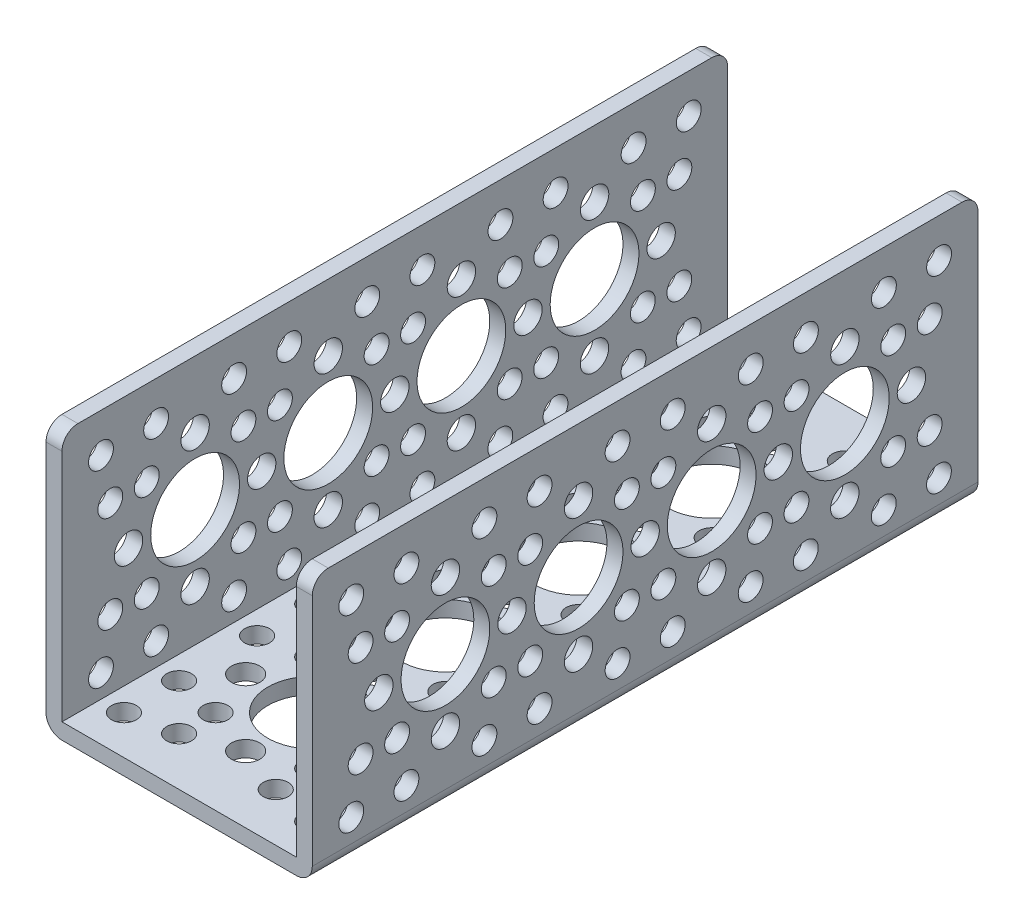
SolidWorks part; units mm, degrees
ref_plane "Front Plane" through (0, 0, 0) normal (0, 0, 1) x (1, 0, 0)
ref_plane "Top Plane" through (0, 0, 0) normal (0, 1, 0) x (1, 0, 0)
ref_plane "Right Plane" through (0, 0, 0) normal (1, 0, 0) x (0, 0, -1)
sketch "Sketch1" plane through (0, 0, 0) normal (0, 0, 1) x (1, 0, 0)
  line L1 (0, 0) -> (38.1, 0)
  line L2 (0, 0) -> (0, 38.1)
  line L4 (38.1, 0) -> (38.1, 38.1)
extrude "Extrude-Thin1" add sketch "Sketch1" along normal blind 95.25 thin thin type one direction wall 2.286
sketch "Sketch3" plane through (0, 0, 0) normal (0, -1, 0) x (1, 0, 0)
  line L0 (19.05, 0) -> (19.05, 95.25) construction
  line L1 (38.1, 0) -> (0, 0) construction
  line L2 (38.1, 95.25) -> (0, 95.25) construction
  circle B0 centre (19.05, 38.1084) radius 6.35
  circle B1 centre (9.525, 38.1084) radius 2.032
  circle B2 centre (28.575, 38.1084) radius 2.032
  circle B3 centre (19.05, 57.1584) radius 6.35
  circle B4 centre (9.525, 57.1584) radius 2.032
  circle B5 centre (28.575, 57.1584) radius 2.032
  circle B6 centre (19.05, 47.625) radius 2.032
  circle B7 centre (25.9648, 50.2352) radius 1.778
  circle B8 centre (32.5204, 43.6796) radius 1.778
  circle B9 centre (12.1352, 50.2352) radius 1.778
  circle B10 centre (5.5796, 43.6796) radius 1.778
  circle B11 centre (25.9648, 45.0148) radius 1.778
  circle B12 centre (12.1352, 45.0148) radius 1.778
  circle B13 centre (32.5204, 51.5704) radius 1.778
  circle B14 centre (5.5796, 51.5704) radius 1.778
  circle B15 centre (19.05, 19.0584) radius 6.35
  circle B16 centre (19.05, 9.5334) radius 2.032
  circle B17 centre (9.525, 19.0584) radius 2.032
  circle B18 centre (19.05, 28.5834) radius 2.032
  circle B19 centre (28.575, 19.0584) radius 2.032
  circle B20 centre (12.1352, 25.9732) radius 1.778
  circle B21 centre (5.5796, 32.5288) radius 1.778
  circle B22 centre (25.9648, 25.9732) radius 1.778
  circle B23 centre (32.5204, 32.5288) radius 1.778
  circle B24 centre (25.9648, 12.1436) radius 1.778
  circle B25 centre (32.5204, 5.588) radius 1.778
  circle B26 centre (12.1352, 12.1436) radius 1.778
  circle B27 centre (5.5796, 5.588) radius 1.778
  circle B28 centre (12.1352, 31.1936) radius 1.778
  circle B29 centre (25.9648, 31.1936) radius 1.778
  circle B30 centre (25.9648, 6.9232) radius 1.778
  circle B31 centre (12.1352, 6.9232) radius 1.778
  circle B32 centre (32.5204, 13.4788) radius 1.778
  circle B33 centre (5.5796, 13.4788) radius 1.778
  circle B34 centre (5.5796, 24.638) radius 1.778
  circle B35 centre (32.5204, 24.638) radius 1.778
  circle B36 centre (19.05, 76.2084) radius 6.35
  circle B37 centre (19.05, 66.6834) radius 2.032
  circle B38 centre (9.525, 76.2084) radius 2.032
  circle B39 centre (19.05, 85.7334) radius 2.032
  circle B40 centre (28.575, 76.2084) radius 2.032
  circle B41 centre (12.1352, 83.1232) radius 1.778
  circle B42 centre (5.5796, 89.6788) radius 1.778
  circle B43 centre (25.9648, 83.1232) radius 1.778
  circle B44 centre (32.5204, 89.6788) radius 1.778
  circle B45 centre (25.9648, 69.2936) radius 1.778
  circle B46 centre (32.5204, 62.738) radius 1.778
  circle B47 centre (12.1352, 69.2936) radius 1.778
  circle B48 centre (5.5796, 62.738) radius 1.778
  circle B49 centre (12.1352, 88.3436) radius 1.778
  circle B50 centre (25.9648, 88.3436) radius 1.778
  circle B51 centre (25.9648, 64.0732) radius 1.778
  circle B52 centre (12.1352, 64.0732) radius 1.778
  circle B53 centre (32.5204, 70.6288) radius 1.778
  circle B54 centre (5.5796, 70.6288) radius 1.778
  circle B55 centre (5.5796, 81.788) radius 1.778
  circle B56 centre (32.5204, 81.788) radius 1.778
  dimension "D1" = 5.588
  dimension "D2" = 19.05
  dimension "D3" = 38.1
  dimension "D4" = 19.05
sketch_block_instance "Actobotics hole pattern c-12"
sketch_block "Actobotics hole pattern c" parameters "D1"=12.7, "D4"=4.064, "D2"=19.05, "D3"=9.525
sketch_block_instance "Actobotics hole pattern c-13"
sketch_block_instance "Actobotics hole pattern 2-4"
sketch_block "Actobotics hole pattern 2" parameters "D1"=4.064
sketch_block_instance "actobotics hole pattern-14"
sketch_block "actobotics hole pattern" parameters "D1"=12.7, "D3"=4.064, "D6"=3.556, "D7"=3.556, "D2"=9.525, "D4"=19.05, "D5"=9.779
sketch_block_instance "actobotics hole pattern-15"
extrude "Cut-Extrude1" cut sketch "Sketch3" against normal up to next (2.286 mm away)
sketch "Sketch4" plane through (0, 0, 0) normal (-1, 0, 0) x (0, 0, 1)
  line L0 (0, 0) -> (0, 38.1) construction
  line L1 (95.25, 0) -> (95.25, 38.1) construction
  line L2 (0, 19.05) -> (95.25, 19.05) construction
  circle B0 centre (57.15, 19.05) radius 6.35
  circle B1 centre (57.15, 28.575) radius 2.032
  circle B2 centre (57.15, 9.525) radius 2.032
  circle B3 centre (38.1, 19.05) radius 6.35
  circle B4 centre (38.1, 28.575) radius 2.032
  circle B5 centre (38.1, 9.525) radius 2.032
  circle B6 centre (47.625, 19.05) radius 2.032
  circle B7 centre (50.2352, 12.1352) radius 1.778
  circle B8 centre (43.6796, 5.5796) radius 1.778
  circle B9 centre (50.2352, 25.9648) radius 1.778
  circle B10 centre (43.6796, 32.5204) radius 1.778
  circle B11 centre (45.0148, 12.1352) radius 1.778
  circle B12 centre (45.0148, 25.9648) radius 1.778
  circle B13 centre (51.5704, 5.5796) radius 1.778
  circle B14 centre (51.5704, 32.5204) radius 1.778
  circle B15 centre (76.2, 19.05) radius 6.35
  circle B16 centre (66.675, 19.05) radius 2.032
  circle B17 centre (76.2, 28.575) radius 2.032
  circle B18 centre (85.725, 19.05) radius 2.032
  circle B19 centre (76.2, 9.525) radius 2.032
  circle B20 centre (83.1148, 25.9648) radius 1.778
  circle B21 centre (89.6704, 32.5204) radius 1.778
  circle B22 centre (83.1148, 12.1352) radius 1.778
  circle B23 centre (89.6704, 5.5796) radius 1.778
  circle B24 centre (69.2852, 12.1352) radius 1.778
  circle B25 centre (62.7296, 5.5796) radius 1.778
  circle B26 centre (69.2852, 25.9648) radius 1.778
  circle B27 centre (62.7296, 32.5204) radius 1.778
  circle B28 centre (88.3352, 25.9648) radius 1.778
  circle B29 centre (88.3352, 12.1352) radius 1.778
  circle B30 centre (64.0648, 12.1352) radius 1.778
  circle B31 centre (64.0648, 25.9648) radius 1.778
  circle B32 centre (70.6204, 5.5796) radius 1.778
  circle B33 centre (70.6204, 32.5204) radius 1.778
  circle B34 centre (81.7796, 32.5204) radius 1.778
  circle B35 centre (81.7796, 5.5796) radius 1.778
  circle B36 centre (19.05, 19.05) radius 6.35
  circle B37 centre (9.525, 19.0441) radius 2.032
  circle B38 centre (19.0441, 28.575) radius 2.032
  circle B39 centre (28.575, 19.0559) radius 2.032
  circle B40 centre (19.0559, 9.525) radius 2.032
  circle B41 centre (25.9605, 25.9691) radius 1.778
  circle B42 centre (32.512, 32.5288) radius 1.778
  circle B43 centre (25.9691, 12.1395) radius 1.778
  circle B44 centre (32.5288, 5.588) radius 1.778
  circle B45 centre (12.1395, 12.1309) radius 1.778
  circle B46 centre (5.588, 5.5712) radius 1.778
  circle B47 centre (12.1309, 25.9605) radius 1.778
  circle B48 centre (5.5712, 32.512) radius 1.778
  circle B49 centre (31.1809, 25.9723) radius 1.778
  circle B50 centre (31.1895, 12.1428) radius 1.778
  circle B51 centre (6.9191, 12.1277) radius 1.778
  circle B52 centre (6.9105, 25.9572) radius 1.778
  circle B53 centre (13.4788, 5.5761) radius 1.778
  circle B54 centre (13.462, 32.5169) radius 1.778
  circle B55 centre (24.6212, 32.5239) radius 1.778
  circle B56 centre (24.638, 5.5831) radius 1.778
  dimension "D1" = 5.588
sketch_block_instance "Actobotics hole pattern c-7"
sketch_block_instance "Actobotics hole pattern c-8"
sketch_block_instance "Actobotics hole pattern 2-1"
sketch_block_instance "actobotics hole pattern-8"
sketch_block_instance "actobotics hole pattern-9"
extrude "Cut-Extrude2" cut sketch "Sketch4" against normal through all
fillet "Fillet1" radius 2.286 6 edges at (1.143, 38.1, 95.25) (36.957, 38.1, 95.25) (36.957, 38.1, 0) (1.143, 38.1, 0) (38.1, 0, 47.625) (0, 0, 47.625)
